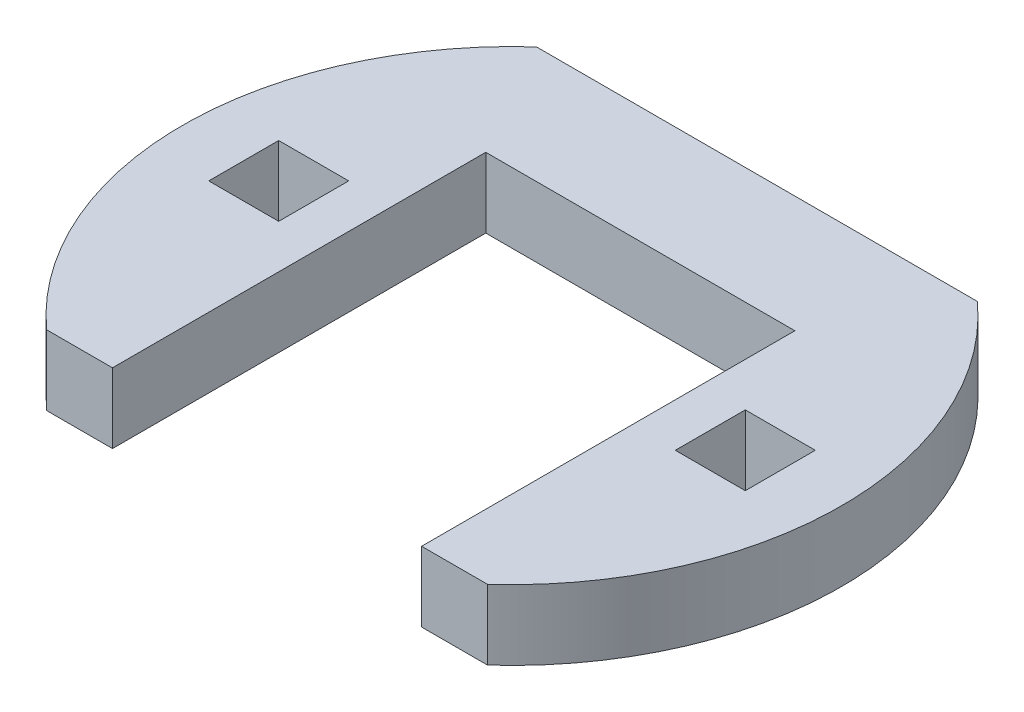
SolidWorks part; units mm, degrees
ref_plane "Alzado" through (0, 0, 0) normal (0, 0, 1) x (1, 0, 0)
ref_plane "Planta" through (0, 0, 0) normal (0, 1, 0) x (1, 0, 0)
ref_plane "Vista lateral" through (0, 0, 0) normal (1, 0, 0) x (0, 0, -1)
sketch "Croquis1" plane through (0, 0, 0) normal (0, 1, 0) x (1, 0, 0)
  line L0 (-161, 103.5) -> (-38.7919, 9.7565)
  line L1 (-40, 40) -> (40, 40) construction
  line L2 (-40, 40) -> (-40, -40) construction
  line L3 (-40, -40) -> (40, -40) construction
  line L4 (40, 40) -> (40, -40) construction
  line L5 (-40, 40) -> (40, -40) construction
  line L6 (-40, -40) -> (40, 40) construction
  line L7 (-161, 123.5) -> (161, 123.5) construction
  line L8 (-161, 123.5) -> (-161, -123.5) construction
  line L9 (-161, -123.5) -> (161, -123.5) construction
  line L10 (161, 123.5) -> (161, -123.5) construction
  line L11 (-161, 123.5) -> (161, -123.5) construction
  line L12 (-161, -123.5) -> (161, 123.5) construction
  line L13 (-161, 103.5) -> (-161, 123.5)
  line L14 (-161, 123.5) -> (-141, 123.5)
  line L15 (-141, 123.5) -> (-22.8238, 32.8493)
  line L16 (-38.7919, -9.7565) -> (-161, -103.5)
  line L17 (-161, -103.5) -> (-161, -123.5)
  line L18 (-161, -123.5) -> (-141, -123.5)
  line L19 (-141, -123.5) -> (-22.8238, -32.8493)
  line L20 (-38.7919, 9.7565) -> (-38.7919, -9.7565) construction
  line L21 (-22.8238, 32.8493) -> (-22.8238, -32.8493) construction
  line L22 (0, 40) -> (0, -40) construction
  line L23 (161, 123.5) -> (141, 123.5)
  line L24 (141, 123.5) -> (22.8238, 32.8493)
  line L25 (161, 103.5) -> (161, 123.5)
  line L26 (161, 103.5) -> (38.7919, 9.7565)
  line L27 (161, -123.5) -> (141, -123.5)
  line L28 (161, -103.5) -> (161, -123.5)
  line L29 (38.7919, -9.7565) -> (161, -103.5)
  line L30 (141, -123.5) -> (22.8238, -32.8493)
  circle A0 centre (0, 0) radius 40 construction
  arc A1 (-38.7919, 9.7565) -> (-38.7919, -9.7565) centre (0, 0) ccw
  arc A2 (-22.8238, 32.8493) -> (22.8238, 32.8493) centre (0, 0) cw
  arc A3 (22.8238, -32.8493) -> (-22.8238, -32.8493) centre (0, 0) cw
  arc A4 (38.7919, 9.7565) -> (38.7919, -9.7565) centre (0, 0) cw
  point P0 (0, 0)
  point P6 (0, 0)
  dimension "D1" = 80
  dimension "D2" = 80
  dimension "D3" = 322
  dimension "D4" = 247
  dimension "D5" = 20
extrude "Saliente-Extruir1" add sketch "Croquis1" along normal blind 6
sketch "Croquis4" plane through (0, 0, 0) normal (0, 1, 0) x (1, 0, 0)
  line L0 (-161, 103.5) -> (-161, 123.5)
  line L1 (-161, 123.5) -> (-141, 123.5)
  line L2 (-141, 123.5) -> (-141, 129.5)
  line L3 (-141, 129.5) -> (-167, 129.5)
  line L4 (-167, 129.5) -> (-167, 103.5)
  line L5 (-167, 103.5) -> (-161, 103.5)
  line L6 (-161, -103.5) -> (-161, -123.5)
  line L7 (-161, -123.5) -> (-141, -123.5)
  line L8 (-141, -123.5) -> (-141, -129.5)
  line L9 (-141, -129.5) -> (-167, -129.5)
  line L10 (-167, -129.5) -> (-167, -103.5)
  line L11 (-167, -103.5) -> (-161, -103.5)
  line L12 (0, 40) -> (0, -40) construction
  line L13 (167, -103.5) -> (161, -103.5)
  line L14 (167, -129.5) -> (167, -103.5)
  line L15 (141, -129.5) -> (167, -129.5)
  line L16 (141, -123.5) -> (141, -129.5)
  line L17 (161, -123.5) -> (141, -123.5)
  line L18 (161, -103.5) -> (161, -123.5)
  line L19 (167, 103.5) -> (161, 103.5)
  line L20 (167, 129.5) -> (167, 103.5)
  line L21 (141, 129.5) -> (167, 129.5)
  line L22 (141, 123.5) -> (141, 129.5)
  line L23 (161, 123.5) -> (141, 123.5)
  line L24 (161, 103.5) -> (161, 123.5)
  arc A0 (22.8238, 32.8493) -> (-22.8238, 32.8493) centre (0, 0) ccw construction
  arc A1 (-22.8238, -32.8493) -> (22.8238, -32.8493) centre (0, 0) ccw construction
  dimension "D1" = 6
  dimension "D2" = 6
  dimension "D3" = 6
  dimension "D4" = 6
extrude "Saliente-Extruir2" [suppressed] add sketch "Croquis4" along normal blind 12
sketch "Croquis7" plane through (0, 0, 0) normal (0, -1, 0) x (-1, 0, 0)
  circle A0 centre (0, 0) radius 40
  arc A1 (-38.7919, 9.7565) -> (-38.7919, -9.7565) centre (0, 0) ccw construction
extrude "Saliente-Extruir5" add sketch "Croquis7" along normal blind 6
sketch "Croquis5" plane through (0, -6, 0) normal (0, -1, 0) x (1, 0, 0)
  line L0 (13.25, 11) -> (-13.25, 11) construction
  line L1 (-10.25, 8) -> (10.25, 8) construction
  line L2 (-10.25, 8) -> (-10.25, -8) construction
  line L3 (-10.25, -8) -> (10.25, -8) construction
  line L4 (10.25, 8) -> (10.25, -8) construction
  line L5 (-10.25, 8) -> (10.25, -8) construction
  line L6 (-10.25, -8) -> (10.25, 8) construction
  line L7 (-13.25, 11) -> (-13.25, -11) construction
  line L8 (-13.25, -11) -> (13.25, -11) construction
  line L9 (13.25, -11) -> (13.25, -21) construction
  line L10 (13.25, -21) -> (-28.25, -21) construction
  line L11 (-28.25, -21) -> (-28.25, 21) construction
  line L12 (-28.25, 21) -> (13.25, 21) construction
  line L13 (13.25, 21) -> (13.25, 11) construction
  line L14 (0, 11) -> (0, 0) construction
  line L15 (0, 0) -> (0, -11) construction
  line L16 (13.25, 11) -> (28.25, 11) construction
  line L17 (-28.25, 21) -> (28.25, 21) construction
  line L18 (-28.25, 21) -> (-28.25, -21) construction
  line L19 (-28.25, -21) -> (28.25, -21) construction
  line L20 (28.25, 21) -> (28.25, -21) construction
  line L21 (-28.25, 21) -> (28.25, -21) construction
  line L22 (-28.25, -21) -> (28.25, 21) construction
  line L23 (28.25, 11) -> (28.25, 21) construction
  line L24 (28.25, 21) -> (13.25, 21) construction
  line L25 (13.25, -21) -> (28.25, -21) construction
  line L26 (28.25, -21) -> (28.25, -11) construction
  line L27 (28.25, -11) -> (13.25, -11) construction
  line L28 (-9, 7) -> (9, 7) construction
  line L29 (0, 7) -> (0, 0) construction
  line L30 (-9, 7) -> (9, 7) construction
  line L31 (-9, 7.5) -> (9, 7.5) construction
  line L32 (-9, 6.5) -> (9, 6.5) construction
  line L33 (-18.8961, 21) -> (18.8961, 21) construction
  line L34 (18.8961, -21) -> (-18.8961, -21)
  line L35 (-18.8961, 21) -> (-13.25, 21)
  line L36 (-13.25, 21) -> (-13.25, -11)
  line L37 (-13.25, -11) -> (13.25, -11)
  line L38 (13.25, -11) -> (13.25, 21)
  line L39 (13.25, 21) -> (18.8961, 21)
  line L40 (-8, -5.75) -> (8, -5.75) construction
  arc A0 (-9, 7.5) -> (-9, 6.5) centre (-9, 7) ccw construction
  arc A1 (9, 6.5) -> (9, 7.5) centre (9, 7) ccw construction
  arc A2 (-18.8961, 21) -> (-18.8961, -21) centre (0, 0) ccw
  arc A3 (18.8961, 21) -> (18.8961, -21) centre (0, 0) cw
  circle A4 centre (-8, -5.75) radius 1.75 construction
  circle A5 centre (8, -5.75) radius 1.75 construction
  point P0 (0, 0)
  point P26 (0, 7)
  dimension "D11" = 0.5
  dimension "D12" = 3.5
  dimension "D14" = 2.25
  dimension "D1" = 16
  dimension "D2" = 20.5
  dimension "D3" = 3
  dimension "D4" = 3
  dimension "D5" = 10
  dimension "D6" = 10
  dimension "D7" = 15
  dimension "D8" = 3
  dimension "D9" = 18
  dimension "D10" = 1
  dimension "D13" = 2.25
  dimension "D15" = 2.25
extrude "Saliente-Extruir3" add sketch "Croquis5" along normal blind 6
sketch "Croquis6" plane through (0, -12, 0) normal (0, -1, 0) x (1, 0, 0)
  line L0 (18.8961, 21) -> (13.25, 21) construction
  line L1 (-28.25, 21) -> (28.25, 21) construction
  line L2 (-28.25, 21) -> (-28.25, -21) construction
  line L3 (-28.25, -21) -> (28.25, -21) construction
  line L4 (28.25, 21) -> (28.25, -21) construction
  line L5 (-28.25, 21) -> (28.25, -21) construction
  line L6 (-28.25, -21) -> (28.25, 21) construction
  line L7 (-18.8961, 21) -> (-13.25, 21)
  line L8 (-9, 7) -> (9, 7) construction
  line L9 (-9, 7.5) -> (9, 7.5) construction
  line L10 (-9, 6.5) -> (9, 6.5) construction
  line L11 (-18.8961, 21) -> (18.8961, 21) construction
  line L12 (18.8961, -21) -> (-18.8961, -21) construction
  line L18 (13.25, 21) -> (18.8961, 21)
  line L19 (18.8961, -21) -> (-18.8961, -21)
  line L20 (-13.25, 21) -> (-13.25, 3.5)
  line L21 (-13.25, 21) -> (-13.25, -11) construction
  line L22 (-12.75, 3) -> (12.75, 3)
  line L23 (13.25, -11) -> (13.25, 21) construction
  line L24 (13.25, 3.5) -> (13.25, 21)
  line L25 (-13.25, 3.5) -> (13.25, 3.5) construction
  arc A0 (-9, 7.5) -> (-9, 6.5) centre (-9, 7) ccw construction
  arc A1 (9, 6.5) -> (9, 7.5) centre (9, 7) ccw construction
  arc A2 (9, 6.5) -> (9, 7.5) centre (9, 7) ccw construction
  circle A3 centre (0, 0) radius 28.25 construction
  arc A4 (18.8961, 21) -> (18.8961, -21) centre (0, 0) cw construction
  arc A5 (-18.8961, -21) -> (-18.8961, 21) centre (0, 0) cw construction
  arc A6 (-18.8961, 21) -> (-18.8961, -21) centre (0, 0) ccw construction
  arc A7 (-18.8961, -21) -> (-18.8961, 21) centre (0, 0) cw
  arc A8 (18.8961, -21) -> (18.8961, 21) centre (0, 0) ccw
  circle A9 centre (-8, -5.75) radius 1.75
  circle A10 centre (8, -5.75) radius 1.75
  circle A11 centre (-8, -5.75) radius 1.75 construction
  circle A12 centre (8, -5.75) radius 1.75 construction
  arc A13 (-13.25, 3.5) -> (-12.75, 3) centre (-12.75, 3.5) ccw
  arc A14 (12.75, 3) -> (13.25, 3.5) centre (12.75, 3.5) ccw
  point P0 (0, 0)
  point P14 (0, 7)
  dimension "D2" = 0.5
  dimension "D1" = 18
extrude "Saliente-Extruir4" add sketch "Croquis6" along normal blind 6
sketch "Croquis8" plane through (0, -18, 0) normal (0, -1, 0) x (1, 0, 0)
  line L0 (-20, 0) -> (0, 0) construction
  line L1 (-23, 3) -> (-17, 3)
  line L2 (-23, 3) -> (-23, -3)
  line L3 (-23, -3) -> (-17, -3)
  line L4 (-17, 3) -> (-17, -3)
  line L5 (-23, 3) -> (-17, -3) construction
  line L6 (-23, -3) -> (-17, 3) construction
  line L7 (0, 0) -> (0, -21) construction
  line L8 (-18.8961, -21) -> (18.8961, -21) construction
  line L9 (23, -3) -> (17, -3)
  line L10 (23, 3) -> (23, -3)
  line L11 (23, 3) -> (17, 3)
  line L12 (17, 3) -> (17, -3)
  point P0 (-20, 0)
  dimension "D1" = 6
  dimension "D2" = 6
  dimension "D3" = 20
extrude "Cortar-Extruir1" cut sketch "Croquis8" against normal through all
sketch "Croquis9" plane through (0, 6, 0) normal (0, 1, 0) x (1, 0, 0)
  line L1 (-161, 123.5) -> (161, 123.5)
  line L2 (-161, 123.5) -> (-161, -123.5)
  line L3 (-161, -123.5) -> (161, -123.5)
  line L4 (161, 123.5) -> (161, -123.5)
  line L5 (-161, 123.5) -> (161, -123.5) construction
  line L6 (-161, -123.5) -> (161, 123.5) construction
  point P0 (0, 0)
extrude "Cortar-Extruir2" cut sketch "Croquis9" against normal blind 12
sketch "Croquis10" plane through (0, -18, 0) normal (0, 1, 0) x (1, 0, 0)
  circle A0 centre (0, 0) radius 28.25
  arc A1 (18.8961, -21) -> (18.8961, 21) centre (0, 0) ccw construction
extrude "Cortar-Extruir3" cut sketch "Croquis10" along normal blind 6
